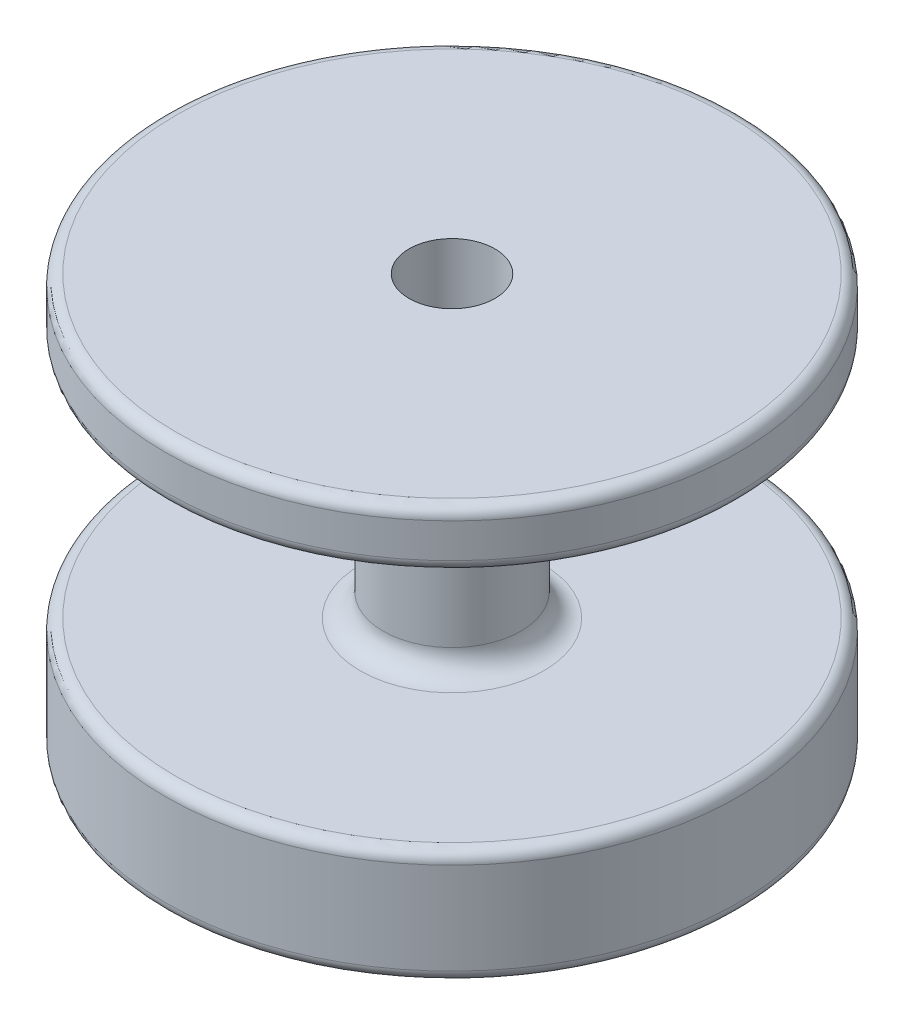
SolidWorks part; units mm, degrees
material "自定义塑料"
ref_plane "前视基准面" through (0, 0, 0) normal (0, 0, 1) x (1, 0, 0)
ref_plane "上视基准面" through (0, 0, 0) normal (0, 1, 0) x (1, 0, 0)
ref_plane "右视基准面" through (0, 0, 0) normal (1, 0, 0) x (0, 0, -1)
sketch "草图1" plane through (0, 0, 0) normal (0, 1, 0) x (1, 0, 0)
  circle A0 centre (0, 0) radius 25
  dimension "D1" = 50
extrude "凸台-拉伸1" add sketch "草图1" along normal blind 36
sketch "草图2" plane through (0, 0, 0) normal (0, 1, 0) x (1, 0, 0)
  circle A0 centre (0, 0) radius 25
  circle A2 centre (0, 0) radius 6
  circle A3 centre (0, 0) radius 1.6513
  dimension "D1" = 12
  dimension "D2" = 50
extrude "切除-拉伸1" cut sketch "草图2" along normal blind 21 from offset 10 contours A0 A2
sketch "草图5" plane through (0, 0, 0) normal (0, 1, 0) x (1, 0, 0)
  circle A0 centre (0, 0) radius 4.5
  dimension "D1" = 9
extrude "凸台-拉伸2" [suppressed] add sketch "草图5" against normal blind 10
sketch "草图4" plane through (0, 0, 0) normal (0, 1, 0) x (1, 0, 0)
  circle A0 centre (0, 0) radius 2
  dimension "D1" = 4
extrude "切除-拉伸3" cut sketch "草图4" against normal blind 47 and the other way blind 47 contours A0
sketch "草图3" plane through (0, 36, 0) normal (0, 1, 0) x (1, 0, 0)
  circle A0 centre (0, 0) radius 3.75
  dimension "D1" = 7.5
extrude "切除-拉伸7" cut sketch "草图3" against normal blind 17
fillet "圆角1" radius 1 4 edges at (0, 36, 25) (0, 31, 25) (0, 10, 25) (0, 0, 25)
fillet "圆角2" radius 2 2 edges at (0, 31, 6) (0, 10, 6)
